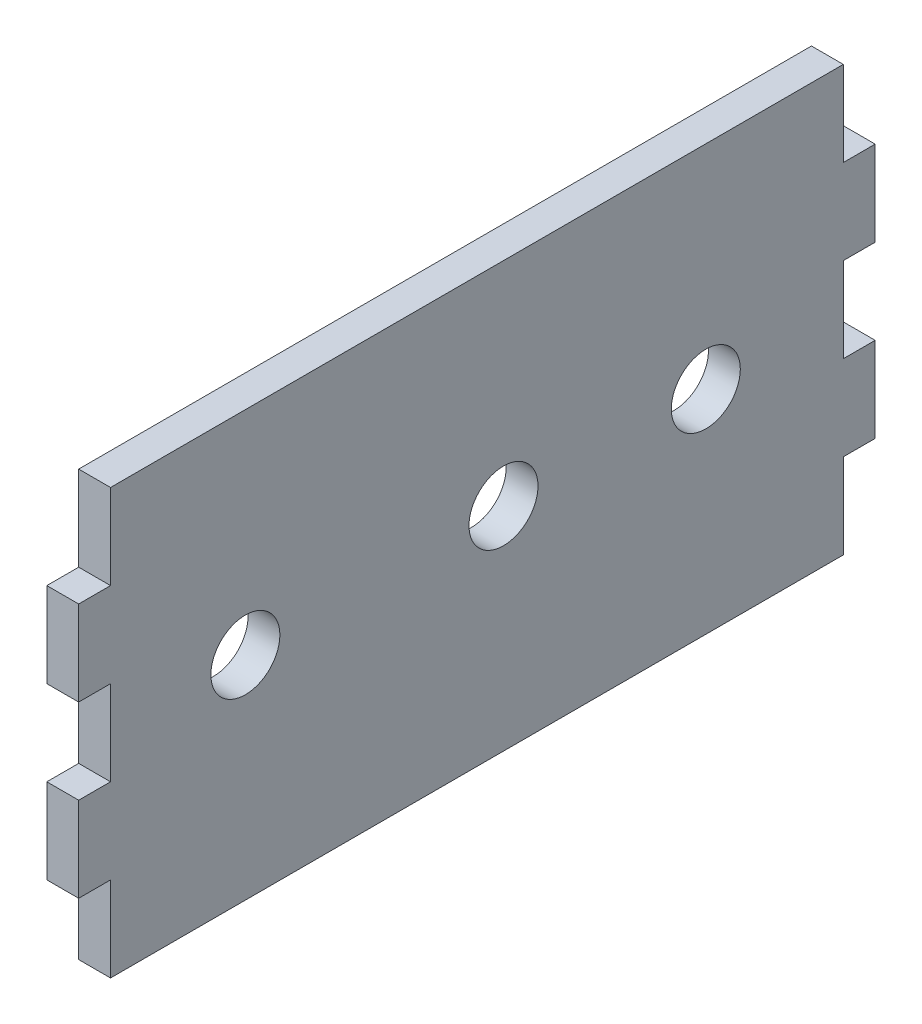
SolidWorks part; units mm, degrees
ref_plane "Alzado" through (0, 0, 0) normal (0, 0, 1) x (1, 0, 0)
ref_plane "Planta" through (0, 0, 0) normal (0, 1, 0) x (1, 0, 0)
ref_plane "Vista lateral" through (0, 0, 0) normal (1, 0, 0) x (0, 0, -1)
sketch "Croquis1" plane through (0, 0, 0) normal (1, 0, 0) x (0, 0, -1)
  line L0 (0, 40) -> (0, -40) construction
  line L1 (75, -40) -> (-75, -40)
  line L2 (75, -40) -> (75, 40)
  line L3 (75, 40) -> (-75, 40)
  line L4 (-75, -40) -> (-75, 40)
  line L5 (75, -40) -> (-75, 40) construction
  line L6 (75, 40) -> (-75, -40) construction
  point P0 (0, 0)
  dimension "D1" = 150
  dimension "D2" = 80
extrude "Saliente-Extruir1" add sketch "Croquis1" along normal blind 6
sketch "Croquis2" plane through (6, 0, 0) normal (1, 0, 0) x (0, 0, -1)
  line L1 (-75, -40) -> (75, -40) construction
  line L2 (-75, 40) -> (-75, -40) construction
  circle A0 centre (-43.61, 0) radius 6.5
  circle A1 centre (5, 0) radius 6.5
  circle A2 centre (43.1, 0) radius 6.5
  dimension "D1" = 13
  dimension "D2" = 80
  dimension "D3" = 40
  dimension "D4" = 40
  dimension "D5" = 40
  dimension "D6" = 48.61
  dimension "D7" = 38.1
extrude "Cortar-Extruir1" cut sketch "Croquis2" against normal blind 6
sketch "Croquis3" plane through (6, 0, 0) normal (1, 0, 0) x (0, 0, -1)
  line L0 (0, 40) -> (0, -40) construction
  line L1 (75, 40) -> (-75, 40) construction
  line L2 (-75, -40) -> (75, -40) construction
  line L4 (0, 0) -> (-75, 0) construction
  line L5 (-75, 40) -> (-69, 40)
  line L6 (-75, 40) -> (-75, 24)
  line L7 (-75, 24) -> (-69, 24)
  line L8 (-69, 40) -> (-69, 24)
  line L9 (-75, 40) -> (-75, -40) construction
  line L10 (-75, -24) -> (-69, -24)
  line L11 (-69, -40) -> (-69, -24)
  line L12 (-75, -40) -> (-69, -40)
  line L13 (-75, -40) -> (-75, -24)
  line L14 (75, -40) -> (75, -24)
  line L15 (75, -40) -> (69, -40)
  line L16 (69, -40) -> (69, -24)
  line L17 (75, -24) -> (69, -24)
  line L18 (75, 24) -> (69, 24)
  line L19 (69, 40) -> (69, 24)
  line L20 (75, 40) -> (69, 40)
  line L21 (75, 40) -> (75, 24)
  line L22 (75, -8) -> (69, -8)
  line L23 (-75, 8) -> (-69, 8)
  line L24 (-75, 8) -> (-75, -8)
  line L25 (-75, -8) -> (-69, -8)
  line L26 (-69, 8) -> (-69, -8)
  line L27 (69, 8) -> (69, -8)
  line L28 (75, 8) -> (69, 8)
  line L29 (75, 8) -> (75, -8)
  point P32 (-72, 8)
  point P33 (-72, -8)
  point P34 (-69, 0)
  dimension "D1" = 16
  dimension "D2" = 6
  dimension "D3" = 8
  dimension "D4" = 8
  dimension "D5" = 6
extrude "Cortar-Extruir2" cut sketch "Croquis3" against normal blind 6
